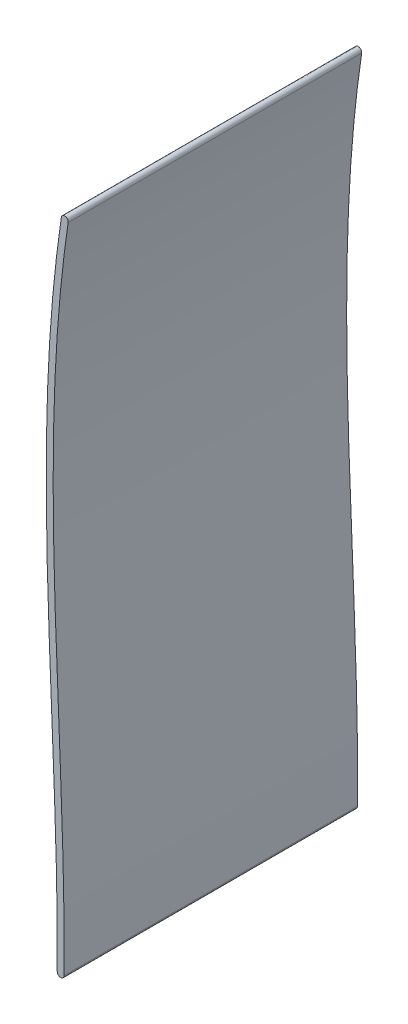
SolidWorks part; units mm, degrees
material "PVC 0.007 Plasticized"
ref_plane "Front Plane" through (0, 0, 0) normal (0, 0, 1) x (1, 0, 0)
ref_plane "Top Plane" through (0, 0, 0) normal (0, 1, 0) x (1, 0, 0)
ref_plane "Right Plane" through (0, 0, 0) normal (1, 0, 0) x (0, 0, -1)
sketch "Sketch1" plane through (0, 0, 0) normal (0, 0, 1) x (1, 0, 0)
  arc A0 (0, 0) -> (1.9999, -0.0145) centre (1, -0.0072) ccw
  arc A1 (1.1822, 189.7438) -> (3.1604, 189.4497) centre (2.1713, 189.5968) cw
  spline S0 degree 3 poles (0, 0) (0.4572, 63.1064) (-8.1624, 126.8801) (1.1822, 189.7438) knots 0 0 0 0 1 1 1 1
  spline S1 degree 1 poles (1.9999, -0.0145) (3.1604, 189.4497) knots 0 0 1 1 construction
  spline S2 degree 3 poles (1.9999, -0.0145) (2.1147, 15.8283) (1.2061, 47.4984) (-1.0208, 95.0478) (-1.4851, 134.5414) (0.2327, 165.9715) (2.0018, 181.6551) (3.1604, 189.4497) knots 0 0 0 0 0.25 0.5 0.75 0.875 1 1 1 1
  dimension "D1" = 190
  dimension "D2" = 1.1822
  dimension "D3" = 2.1973
  dimension "D4" = 2.5241
  dimension "D5" = 79.0477
  dimension "D6" = 151.1577
  dimension "D7" = 2
extrude "Boss-Extrude1" add sketch "Sketch1" along normal blind 85
